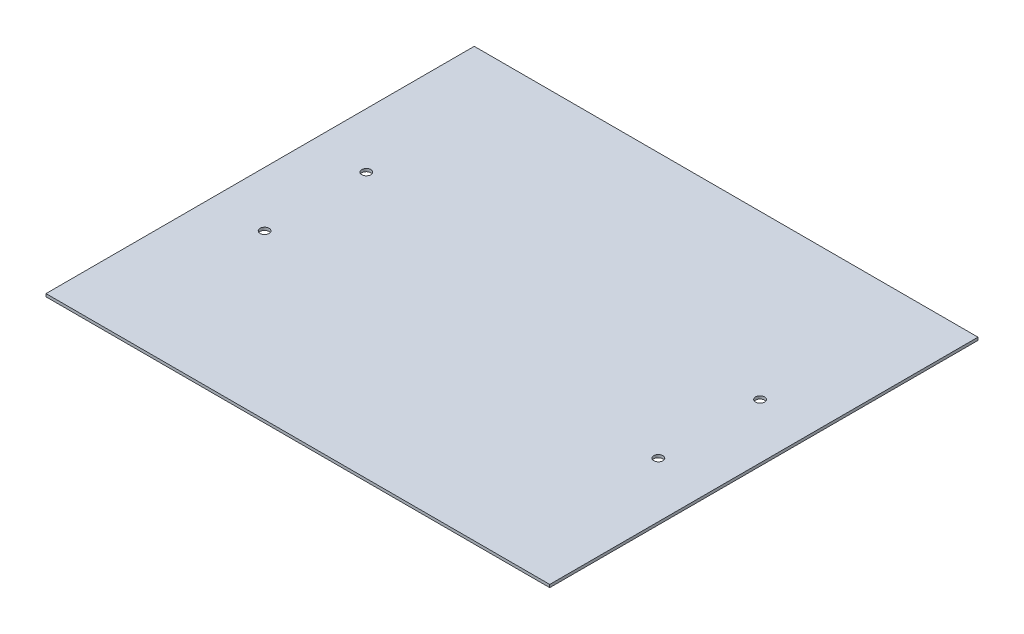
SolidWorks part; units mm, degrees
material "Acrylic (Medium-high impact)"
ref_plane "Front Plane" through (0, 0, 0) normal (0, 0, 1) x (1, 0, 0)
ref_plane "Top Plane" through (0, 0, 0) normal (0, 1, 0) x (1, 0, 0)
ref_plane "Right Plane" through (0, 0, 0) normal (1, 0, 0) x (0, 0, -1)
sketch "Sketch1" plane through (0, 0, 0) normal (0, 1, 0) x (1, 0, 0)
  line L1 (-292.1, 251.1933) -> (292.1, 251.1933)
  line L2 (-292.1, 251.1933) -> (-292.1, -251.1933)
  line L3 (-292.1, -251.1933) -> (292.1, -251.1933)
  line L4 (292.1, 251.1933) -> (292.1, -251.1933)
  line L5 (-292.1, 251.1933) -> (292.1, -251.1933) construction
  line L6 (-292.1, -251.1933) -> (292.1, 251.1933) construction
  point P0 (0, 0)
  dimension "D1" = 584.2
  dimension "D2" = 502.3866
extrude "TopPlate" add sketch "Sketch1" along normal blind 3.0734
sketch "Sketch2" plane through (0, 3.0734, 0) normal (0, 1, 0) x (1, 0, 0)
  line L0 (-213.36, 238.5949) -> (-292.1, 238.5949) construction
  line L1 (-292.1, 251.1933) -> (-292.1, -251.1933) construction
  line L2 (-213.36, 251.1933) -> (-213.36, 248.1199) construction
  line L3 (292.1, 251.1933) -> (-292.1, 251.1933) construction
  line L4 (-213.36, 248.1199) -> (-213.36, 229.0699) construction
  line L5 (-213.36, -237.8583) -> (-213.36, 238.5949) construction
  line L7 (-213.36, -247.3833) -> (-213.36, -250.5583) construction
  line L8 (-213.36, -250.5583) -> (-213.36, -253.7333) construction
  line L9 (-213.36, -247.3833) -> (-213.36, -228.3333) construction
  line L10 (-213.36, -253.7333) -> (-213.36, -256.8067) construction
  circle A0 centre (-213.36, 238.5949) radius 2.8956
  circle A1 centre (-213.36, -237.8583) radius 2.8956
  dimension "D2" = 5.7912
  dimension "D1" = 78.74
  dimension "D3" = 19.05
  dimension "D4" = 3.0734
  dimension "D5" = 19.05
  dimension "D6" = 3.175
  dimension "D7" = 3.0734
  dimension "D8" = 508
extrude "Front/RearTopHoles" cut sketch "Sketch2" against normal through all
pattern_linear "LPattern1" count 4 spacing 142.24 along (1, 0, 0) of "Front/RearTopHoles"
sketch "Sketch3" plane through (0, 3.0734, 0) normal (0, 1, 0) x (1, 0, 0)
  line L0 (-292.1, 165.6715) -> (-289.0266, 165.6715) construction
  line L1 (-292.1, 251.1933) -> (-292.1, -251.1933) construction
  line L2 (-289.0266, 165.6715) -> (-269.9766, 165.6715) construction
  line L3 (292.1, 251.1933) -> (-292.1, 251.1933) construction
  line L4 (292.1, 165.6715) -> (289.0266, 165.6715) construction
  line L5 (292.1, -251.1933) -> (292.1, 251.1933) construction
  line L6 (289.0266, 165.6715) -> (269.9766, 165.6715) construction
  line L7 (-279.5016, 251.1933) -> (-279.5016, 248.1199) construction
  line L8 (-279.5016, 248.1199) -> (-279.5016, 229.0699) construction
  circle A0 centre (-279.5016, 165.6715) radius 2.8956
  circle A1 centre (279.5016, 165.6715) radius 2.8956
  dimension "D3" = 19.05
  dimension "D1" = 5.7912
  dimension "D2" = 3.0734
  dimension "D5" = 3.0734
  dimension "D6" = 19.05
  dimension "D4" = 63.3984
extrude "Cut-Extrude2" cut sketch "Sketch3" against normal through all
pattern_linear "LPattern2" count 4 spacing 110.2021 along (0, 0, 1) of "Cut-Extrude2"
hole_wizard "3/8 Clearance Hole1" positions "Sketch4" profile "Sketch5" hole size "3/8" standard "ANSI Inch" end condition through all
sketch "Sketch4" plane through (0, 3.0734, 0) normal (0, 1, 0) x (1, 0, 0)
  line L0 (-292.1, 0) -> (292.1, 0) construction
  line L1 (-292.1, 251.1933) -> (-292.1, -251.1933) construction
  line L2 (292.1, -251.1933) -> (292.1, 251.1933) construction
  line L5 (0, 251.1933) -> (0, -251.1933) construction
  line L6 (292.1, 251.1933) -> (-292.1, 251.1933) construction
  line L7 (-292.1, -251.1933) -> (292.1, -251.1933) construction
  line L21 (-279.5016, 55.4694) -> (-213.36, 55.4694) construction
  line L24 (-213.36, 238.5949) -> (-213.36, 55.4694) construction
  point P27 (-213.36, 55.4694)
  point P90 (-213.36, -54.7328)
  point P99 (213.36, -54.7328)
  point P100 (213.36, 55.4694)
sketch "Sketch5" plane through (-213.36, 3.0734, -55.4694) normal (1, 0, 0) x (0, 0, 1)
  line L0 (0, 0) -> (0, 3.0734)
  line L1 (0, 3.0734) -> (4.9022, 3.0734)
  line L2 (4.9022, 3.0734) -> (4.9022, 0)
  line L5 (4.9022, 0) -> (0, 0)
  line L11 (0, -6.35) -> (0, 107.95) construction
  dimension "Thru Hole Dia." = 9.8044
  dimension "Thru Hole Depth" = 3.0734
sketch "Sketch7" plane through (0, 3.0734, 0) normal (0, 1, 0) x (1, 0, 0)
  line L0 (-272.9738, -232.0671) -> (-272.9738, 232.0671)
  line L1 (-292.1, -251.1933) -> (292.1, -251.1933)
  line L2 (-292.1, -251.1933) -> (-292.1, 251.1933)
  line L3 (-292.1, 251.1933) -> (292.1, 251.1933)
  line L4 (292.1, -251.1933) -> (292.1, 251.1933)
  line L5 (-272.9738, 232.0671) -> (272.9738, 232.0671)
  line L6 (272.9738, -232.0671) -> (272.9738, 232.0671)
  line L7 (-272.9738, -232.0671) -> (272.9738, -232.0671)
  dimension "D1" = 19.1262
extrude "Cut-Extrude3" cut sketch "Sketch7" against normal through all
equation "\"Height\"= 32in"
equation "\"Width\"= 23in"
equation "\"Depth\"= 20in"
equation "\"Plexi\"= .121in"
equation "\"Boxsize\" = .75in"
equation "\"Boxinner\" = .625in"
equation "\"CornerCube\" = 0.75in"
equation "\"Cutwidth\"= .016in"
equation "\"Earsize\"= 1in + \"Cutwidth\" /2"
equation "\"Slotsize\" = 1in - \"CutWidth\" / 2"
equation "\"InnerWidth\" = \"Width\" - 2* \"Plexi\""
equation "\"InnerHeight\" = \"Height\" -2 * \"Plexi\""
equation "\"InnerDepth\" = \"Depth\" - 2*\"Plexi\""
equation "\"RearNumHoles\" = 4"
equation "\"RearHolesBorder\" = 2.25"
equation "\"RearHoleSpacing\" = (\"Width\" - 2*\"RearHolesBorder\") / (\"RearNumHoles\"-1)"
equation "\"RearBarLength\" = (\"InnerWidth\"-2*\"CornerCube\")"
equation "\"RearTopNumHoles\" = 4"
equation "\"RearTopHolesBorder\" = 3.1"
equation "\"RearTopHolesSpacing\" = (\"Width\" - 2*\"RearTopHolesBorder\") / (\"RearTopNumHoles\"-1)"
equation "\"SideVertNumHoles\" = 4"
equation "\"SideVertHolesBorder\" = \"CornerCube\"+\"FingerLength\"+1.50"
equation "\"SideVertHoleSpacing\" = (\"InnerHeight\" - 2*\"SideVertHolesBorder\") / (\"SideVertNumHoles\"-1)"
equation "\"RivetDia\" = .228in"
equation "\"SlotDepth\" = \"Plexi\" + 0.75in + .005in"
equation "\"SideSlotWidth\"   = \"Plexi\"+.005in"
equation "\"SidePanelVertSpacing\" = (\"Height\"-2*(1.75-\"Plexi\")) / 5"
equation "\"BottomPanelSideHoleSpacing\" = (\"InnerDepth\"-2*(1.75-\"Plexi\")) / 4"
equation "\"D1@Sketch1\"=\"Width\""
equation "\"D2@Sketch1\"=\"TopDepth\""
equation "\"FrontDoorGap\" = .1in"
equation "\"TopDepth\" = \"Depth\"-\"DoorPlexi\"-\"FrontDoorGap\""
equation "\"D1@Sketch2\"=\"RearTopHolesBorder\""
equation "\"D2@Sketch2\"=\"RivetDia\""
equation "\"D3@Sketch2\"=\"Boxsize\""
equation "\"D4@Sketch2\"=\"Plexi\""
equation "\"D5@Sketch2\"=\"Boxsize\""
equation "\"MagnetThickness\"= 0.125in"
equation "\"MagnetDiameter\"= 12mm"
equation "\"D6@Sketch2\"=\"MagnetThickness\""
equation "\"DoorPlexi\" = \"Plexi\""
equation "\"D7@Sketch2\"=\"DoorPlexi\""
equation "\"D8@Sketch2\"=\"Depth\""
equation "\"D3@LPattern1\"=\"RearTopHolesSpacing\""
equation "\"D1@LPattern1\"=\"RearTopNumHoles\""
equation "\"D1@Sketch3\"=\"RivetDia\""
equation "\"D2@Sketch3\"=\"Plexi\""
equation "\"D3@Sketch3\"=\"Boxsize\""
equation "\"FingerLength\" = 1.125in"
equation "\"SideTopNumHoles\" = 4"
equation "\"SideTopHoleOffset\"=\"CornerCube\"+\"FingerLength\"+\"Plexi\"+.5"
equation "\"SideTopHoleSpacing\" = (\"TopBarDepth\"-2*\"SideTopHoleOffset\") / (\"SideTopNumHoles\"-1)"
equation "\"SideHorizNumHoles\" = 4"
equation "\"SideHorizHoleBorder\" = 1.50"
equation "\"SideHorizHoleSpacing\" = (\"TopBarDepth\"-2*\"SideHorizHoleBorder\") / (\"SideHorizNumHoles\"-1)"
equation "\"TopBarDepth\" = \"Depth\"-\"DoorPlexi\"-\"Plexi\"-2*\"MagnetThickness\"-2*\"CornerCube\""
equation "\"D4@Sketch3\"=\"SideTopHoleOffset\""
equation "\"D3@LPattern2\"=\"SideTopHoleSpacing\""
equation "\"D1@LPattern2\"=\"SideTopNumHoles\""
equation "\"D5@Sketch3\"=\"Plexi\""
equation "\"D6@Sketch3\"=\"CornerCube\""
equation "\"EBWidth\" = 9in"
equation "\"BasePlateThickness\" = 0.5in"
equation "\"BasePlateWidth\" = \"Width\"+\"EBWidth\"-2*\"Plexi\""
equation "\"BasePlateDepth\" = \"TopBarDepth\"+2*\"CornerCube\""
equation "\"BoxsizeHalf\" = \"Boxsize\"/2"
equation "\"FingerWidth\" = .625in"
equation "\"SideVertBarLength\"=\"Height\"-\"BasePlateThickness\"-2*\"CornerCube\"-\"Plexi\""
equation "\"RearSideVertNumHoles\" = 4"
equation "\"RearSideVertHolesBorder\" = 2.4"
equation "\"RearSideVertHoleSpacing\" = (\"InnerHeight\" - 2*\"RearSideVertHolesBorder\") / (\"RearSideVertNumHoles\"-1)"
equation "\"CoolerDepth\" = 12in"
equation "\"ShelfGap\" = 0.5in"
equation "\"ShelfDepth\" = \"TopBarDepth\"+\"CornerCube\"-\"CoolerDepth\""
equation "\"ShelfBarDepth\"=\"ShelfDepth\"-2*\"CornerCube\""
equation "\"ShelfWidth\" = \"EBWidth\"-\"ShelfGap\""
equation "\"ShelfBarWidth\" = \"EBWidth\"-\"Boxsize\""
equation "\"ShelfBarWidthShort\" = \"ShelfBarWidth\"-\"Boxsize\"-\"ShelfGap\""
equation "\"IntakeWidth\"=4in"
equation "\"IntakeHeight\"=2in"
equation "\"ExhaustWidth\"=4in"
equation "\"ExhaustHeight\"=2in"
equation "\"VentSpacing\"=7in"
equation "\"AngleBracketLength\"=20mm"
equation "\"AngleBracketWidth\"=.5in"
equation "\"AngleBracketThickness\"=.125in"
equation "\"AngleBracketHolePos\"=15mm"
equation "\"AngleBracketHoleDia\"=\"Rivet3_16Dia\""
equation "\"ShelfBarAngleHole\"=\"ShelfGap\"+\"Boxsize\"+\"AngleBracketHolePosShort\""
equation "\"D1@TopPlate\"=\"Plexi\""
